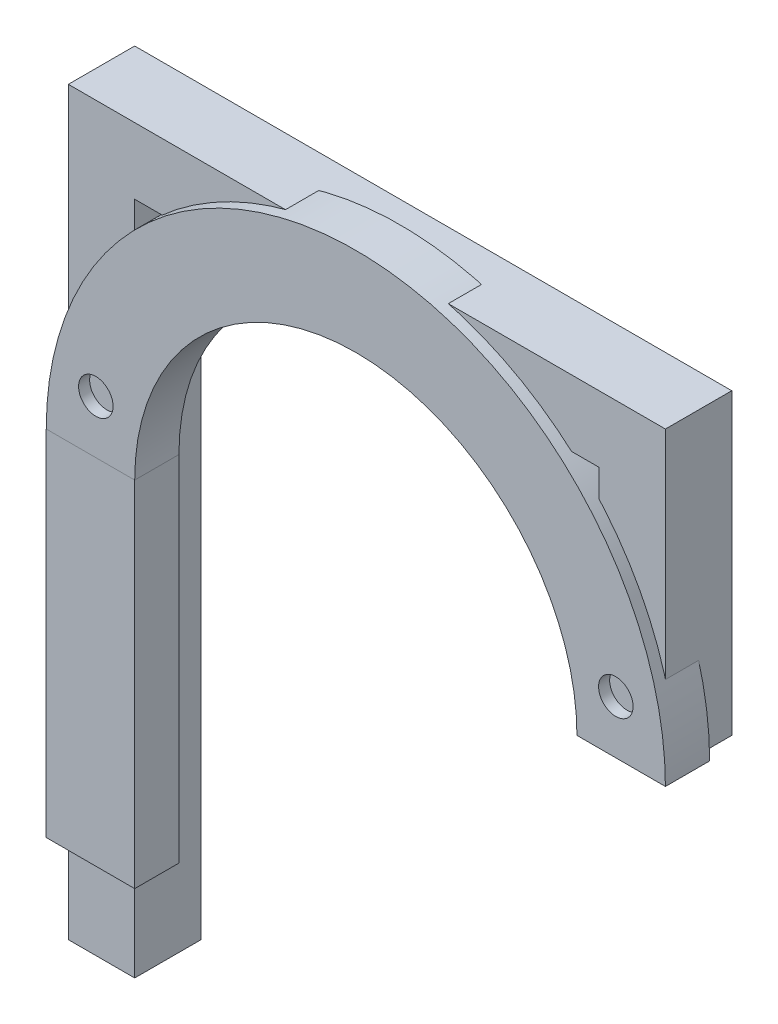
SolidWorks part; units mm, degrees
material "1060 Alloy"
ref_plane "Front Plane" through (0, 0, 0) normal (0, 0, 1) x (1, 0, 0)
ref_plane "Top Plane" through (0, 0, 0) normal (0, 1, 0) x (1, 0, 0)
ref_plane "Right Plane" through (0, 0, 0) normal (1, 0, 0) x (0, 0, -1)
sketch "Sketch8" plane through (0, 0, 0) normal (0, 0, 1) x (1, 0, 0)
  line L0 (0, 0) -> (0, 101.6)
  line L1 (0, 101.6) -> (76.2, 101.6)
  line L2 (76.2, 101.6) -> (76.2, 63.5)
  dimension "D1" = 101.6
  dimension "D2" = 76.2
  dimension "D3" = 38.1
extrude "Extrude-Thin3" add sketch "Sketch8" along normal mid plane 9.525 separate body thin thin type mid plane wall 9.525
sketch "Sketch37" plane through (0, 0, 0) normal (0, 0, 1) x (1, 0, 0)
  line L0 (0, 0) -> (0, 63.5)
  arc A1 (0, 63.5) -> (76.2, 63.5) centre (38.1, 63.5) cw
  dimension "D1" = 38.1
  dimension "D2" = 63.5
  dimension "D3" = 76.2
sketch "Sketch38" plane through (0, 0, 0) normal (0, 1, 0) x (1, 0, 0)
  line L1 (-6.35, 0) -> (6.35, 0)
  line L2 (-6.35, 0) -> (-6.35, -6.35)
  line L3 (-6.35, -6.35) -> (6.35, -6.35)
  line L4 (6.35, 0) -> (6.35, -6.35)
  line L5 (-6.35, 0) -> (6.35, -6.35) construction
  line L6 (-6.35, -6.35) -> (6.35, 0) construction
  point P0 (0, 0)
  point P8 (0, 0)
  dimension "D1" = 6.35
  dimension "D2" = 12.7
sweep "Sweep5" add profiles "Sketch38" path "Sketch37"
sketch "Sketch39" plane through (0, 0, 0) normal (0, 0, 1) x (1, 0, 0)
  line L0 (81.6519, 72.39) -> (69.2085, 69.85) construction
  line L1 (38.1, 63.5) -> (38.1, 107.95) construction
  circle A0 centre (75.4302, 71.12) radius 2.4765
  arc A1 (82.55, 63.5) -> (-6.35, 63.5) centre (38.1, 63.5) ccw construction
  arc A2 (69.85, 63.5) -> (6.35, 63.5) centre (38.1, 63.5) ccw construction
  circle A3 centre (0.7698, 71.12) radius 2.4765
  point P14 (75.4302, 71.12)
  dimension "D1" = 4.953
  dimension "D3" = 12.7
  dimension "D2" = 6.35
extrude "Cut-Extrude1" cut sketch "Sketch39" along normal through all
sketch "Sketch42" plane through (0, 0, 0) normal (0, -1, 0) x (1, 0, 0)
  line L1 (-6.35, 6.35) -> (6.35, 6.35)
  line L2 (-6.35, 6.35) -> (-6.35, 0)
  line L3 (-6.35, 0) -> (6.35, 0)
  line L4 (6.35, 6.35) -> (6.35, 0)
extrude "Cut-Extrude2" cut sketch "Sketch42" against normal blind 12.7
sketch "Sketch43" plane through (0, 12.7, 0) normal (0, -1, 0) x (1, 0, 0)
  line L0 (-6.35, 0) -> (6.35, 0) construction
  line L1 (-4.7625, 0) -> (4.7625, 0)
  line L2 (-4.7625, 0) -> (-4.7625, 4.7625)
  line L3 (-4.7625, 4.7625) -> (4.7625, 4.7625)
  line L4 (4.7625, 0) -> (4.7625, 4.7625)
  line L5 (6.35, 0) -> (6.35, 6.35) construction
  dimension "D1" = 4.7625
  dimension "D2" = 9.525
  dimension "D3" = 1.5875
extrude "Boss-Extrude4" add sketch "Sketch43" along normal blind 12.7
sketch "Sketch45" plane through (0, 0, 0) normal (0, 0, -1) x (-1, 0, 0)
  line L0 (4.7625, 0) -> (4.7625, 12.7) construction
  circle A0 centre (0, 6.35) radius 2.4765
  point P5 (4.7625, 6.35)
  dimension "D1" = 4.953
extrude "Cut-Extrude4" cut sketch "Sketch45" against normal through all
